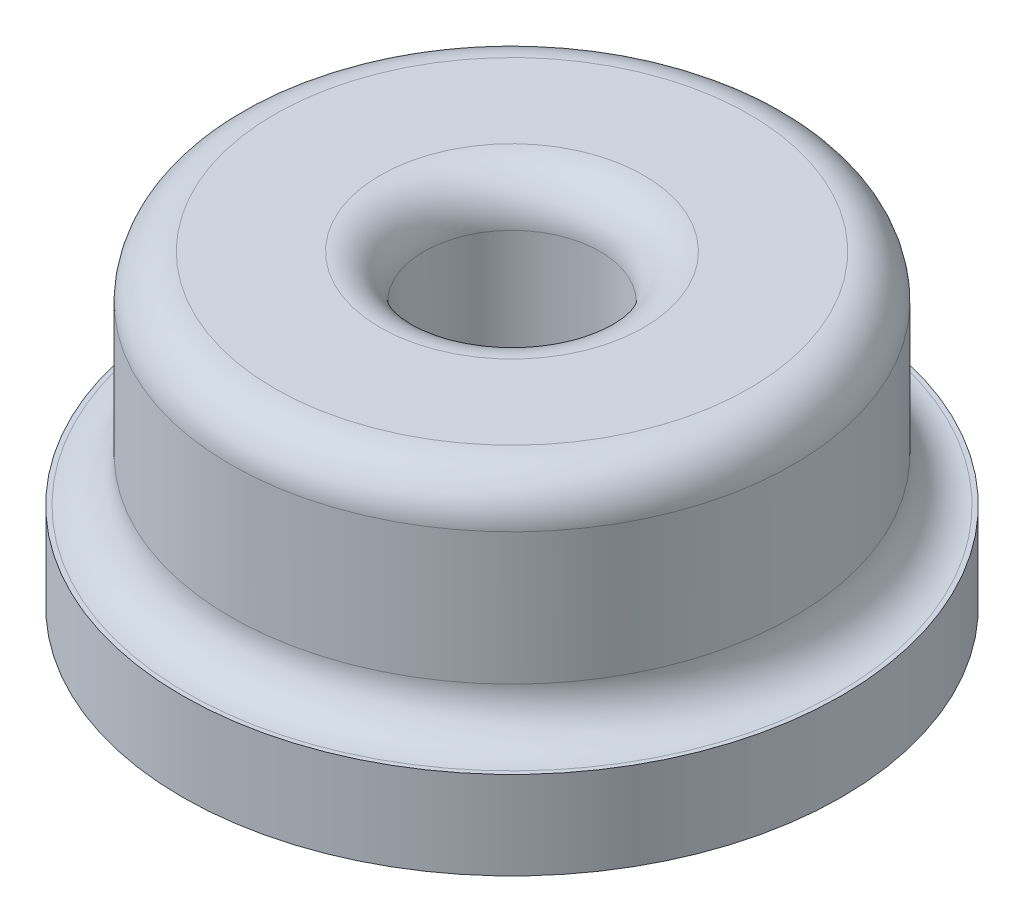
SolidWorks part; units mm, degrees
ref_plane "Front" through (0, 0, 0) normal (0, 0, 1) x (1, 0, 0)
ref_plane "Top" through (0, 0, 0) normal (0, 1, 0) x (1, 0, 0)
ref_plane "Right" through (0, 0, 0) normal (1, 0, 0) x (0, 0, -1)
sketch "草图1" plane through (0, 0, 0) normal (0, 1, 0) x (1, 0, 0)
  circle A0 centre (0, 0) radius 6.4
  dimension "D1" = 12.8
extrude "凸台-拉伸1" add sketch "草图1" along normal blind 5
sketch "草图3" plane through (0, 0, 0) normal (0, -1, 0) x (1, 0, 0)
  circle A0 centre (0, 0) radius 7.5
  dimension "D1" = 15
extrude "凸台-拉伸2" add sketch "草图3" along normal blind 2
sketch "草图2" plane through (0, 5, 0) normal (0, 1, 0) x (1, 0, 0)
  circle A0 centre (0, 0) radius 2
  dimension "D1" = 4
extrude "切除-拉伸1" cut sketch "草图2" against normal through all
fillet "圆角1" radius 1 2 edges at (0, 5, 6.4) (0, 5, 2)
fillet "圆角2" radius 1 1 edges at (0, 0, 6.4)
fillet "圆角3" radius 1 1 edges at (0, -2, 2)
